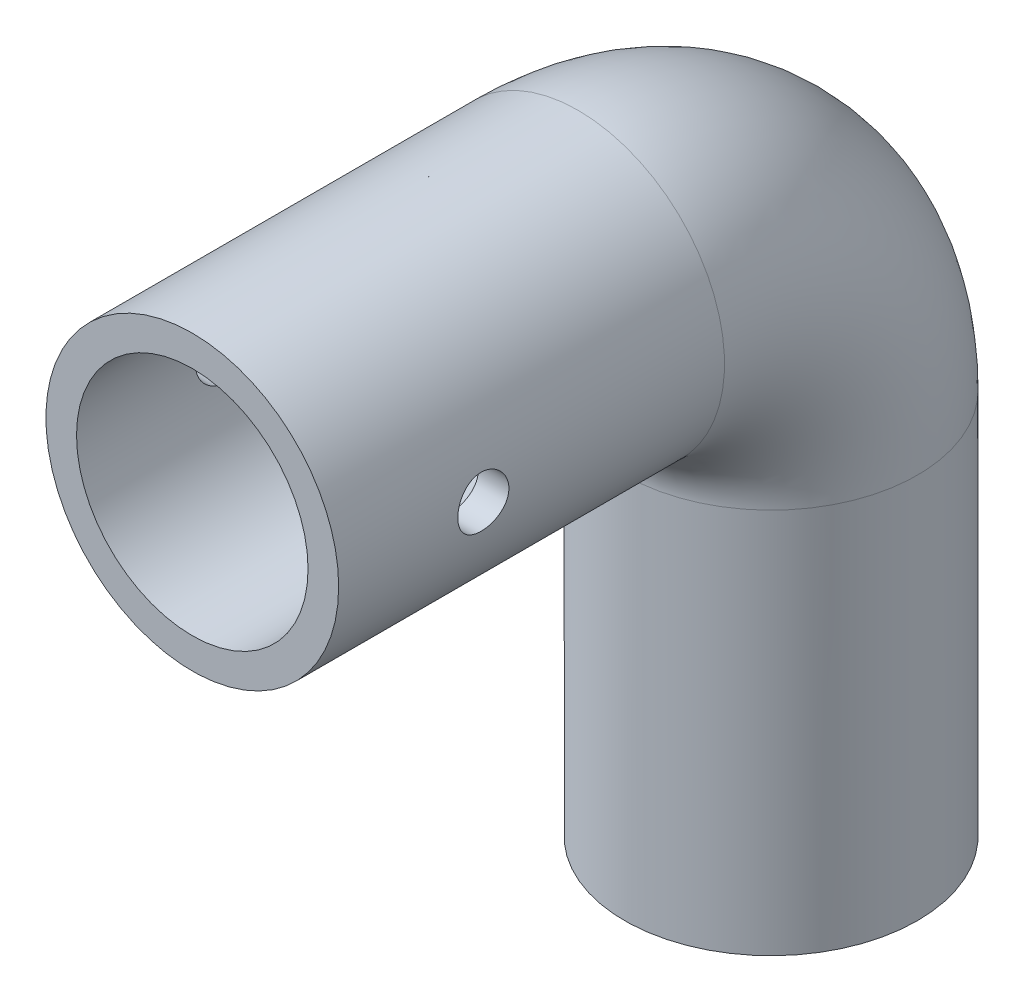
SolidWorks part; units mm, degrees
ref_plane "Front Plane" through (0, 0, 0) normal (0, 0, 1) x (1, 0, 0)
ref_plane "Top Plane" through (0, 0, 0) normal (0, 1, 0) x (1, 0, 0)
ref_plane "Right Plane" through (0, 0, 0) normal (1, 0, 0) x (0, 0, -1)
sketch "Sketch1" plane through (0, 0, 0) normal (0, 0, 1) x (1, 0, 0)
  line L0 (0, 12) -> (0, 15.175) construction
  circle A0 centre (0, 0) radius 12
  circle A1 centre (0, 0) radius 15.175
  dimension "D1" = 24
  dimension "D2" = 3.175
sketch "Sketch3" plane through (0, 0, 0) normal (1, 0, 0) x (0, 0, -1)
  line L0 (0, 0) -> (40, 0)
  line L1 (60, -20) -> (60, -60)
  arc A0 (40, 0) -> (60, -20) centre (40, -20) cw
  point P6 (60, 0)
  dimension "D3" = 20
  dimension "D1" = 60
  dimension "D2" = 60
sweep "Sweep1" add profiles "Sketch1" path "Sketch3"
sketch "Sketch4" plane through (0, 0, 0) normal (1, 0, 0) x (0, 0, -1)
  line L0 (0, 0) -> (15, 0) construction
  line L1 (60, -60) -> (60, -45) construction
  line L2 (44.825, -60) -> (75.175, -60) construction
  dimension "D1" = 15
  dimension "D2" = 15
hole_wizard "M5 Clearance Hole1" positions "Sketch5" profile "Sketch6" hole size "M5" standard "ANSI Metric"
sketch "Sketch5" plane through (0, 0, 0) normal (1, 0, 0) x (0, 0, -1)
  point P0 (15, 0)
sketch "Sketch6" plane through (0, 0, -15) normal (0, 1, 0) x (0, 0, 1)
  line L0 (0, 0) -> (0, 15.175)
  line L1 (0, 15.175) -> (2.65, 15.175)
  line L2 (2.65, 15.175) -> (2.65, 0)
  line L5 (2.65, 0) -> (0, 0)
  line L11 (0, -6.35) -> (0, 107.95) construction
  dimension "Thru Hole Dia." = 5.3
  dimension "Thru Hole Depth" = 15.175
mirror "Mirror1" about plane through (0, 0, 0) normal (1, 0, 0) of "M5 Clearance Hole1"
equation "\"tubeOutDiameter\" = 35mm"
equation "\"wheelShaftDiameter\"= 12mm"
equation "\"wheelThickness\"= 135mm"
equation "\"BearingDiameter\"= 20mm"
equation "\"BearingThickness\"= 10mm"
equation "\"frontShaftDiameter\"= 20mm"
equation "\"D1@Sketch1\"=\"wheelShaftDiameter\"*2"
